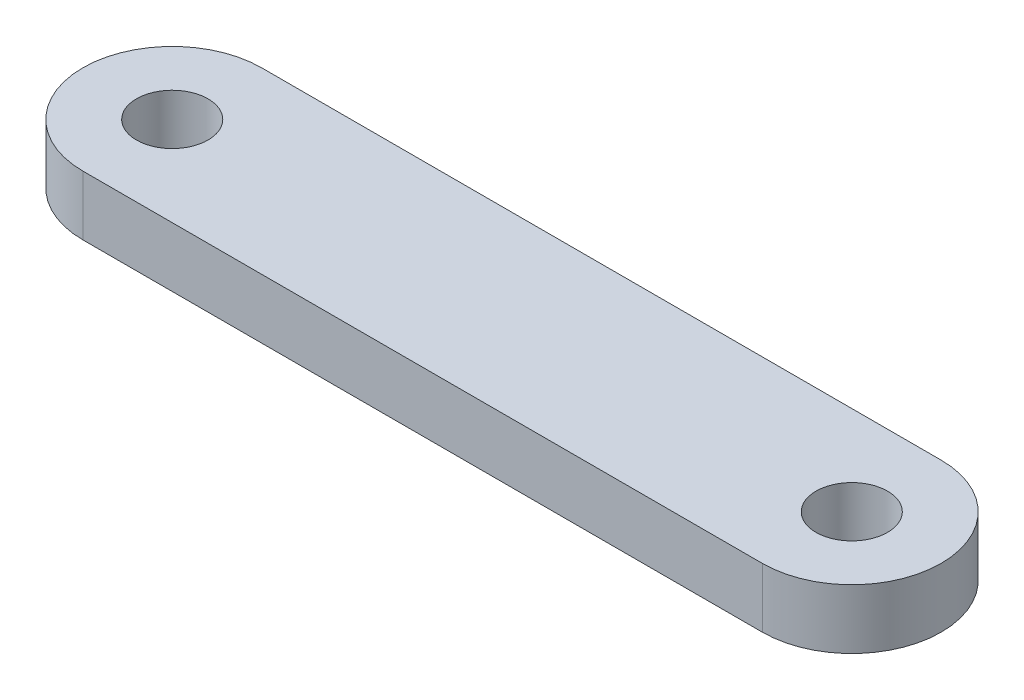
SolidWorks part; units mm, degrees
ref_plane "Front Plane" through (0, 0, 0) normal (0, 0, 1) x (1, 0, 0)
ref_plane "Top Plane" through (0, 0, 0) normal (0, 1, 0) x (1, 0, 0)
ref_plane "Right Plane" through (0, 0, 0) normal (1, 0, 0) x (0, 0, -1)
sketch "Sketch1" plane through (0, 0, 0) normal (0, 1, 0) x (1, 0, 0)
  line L0 (0, 7.5) -> (57, 7.5)
  line L1 (0, -7.5) -> (57, -7.5)
  arc A0 (0, 7.5) -> (0, -7.5) centre (0, 0) ccw
  arc A1 (57, -7.5) -> (57, 7.5) centre (57, 0) ccw
  circle A2 centre (57, 0) radius 3
  circle A3 centre (0, 0) radius 3
  point P8 (0, 0)
  dimension "D1" = 15
  dimension "D3" = 6
  dimension "D4" = 6
  dimension "D2" = 57
extrude "Boss-Extrude1" add sketch "Sketch1" along normal blind 5
